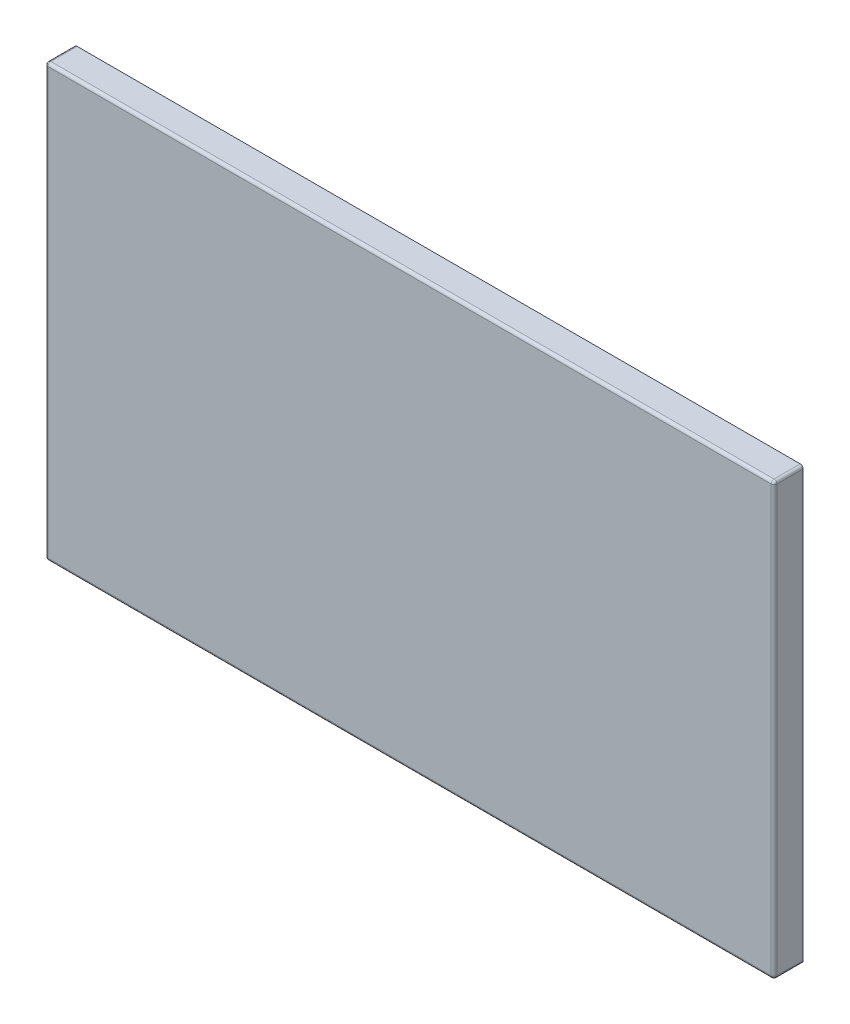
SolidWorks part; units mm, degrees
material "Glass"
ref_plane "Front Plane" through (0, 0, 0) normal (0, 0, 1) x (1, 0, 0)
ref_plane "Top Plane" through (0, 0, 0) normal (0, 1, 0) x (1, 0, 0)
ref_plane "Right Plane" through (0, 0, 0) normal (1, 0, 0) x (0, 0, -1)
sketch "Sketch1" plane through (0, 0, 0) normal (0, 0, 1) x (1, 0, 0)
  line L0 (0, 0) -> (2500, 0)
  line L1 (2500, 0) -> (2500, 1480)
  line L2 (2500, 1480) -> (0, 1480)
  line L3 (0, 1480) -> (0, 0)
  dimension "D1" = 2500
  dimension "D2" = 1480
extrude "Boss-Extrude1" add sketch "Sketch1" along normal blind 100
shell "Shell1" thickness 20
fillet "Fillet1" radius 10 8 edges at (1250, 1480, 100) (2500, 740, 100) (1250, 0, 100) (0, 740, 100) (0, 0, 50) (0, 1480, 50) (2500, 1480, 50) (2500, 0, 50)
